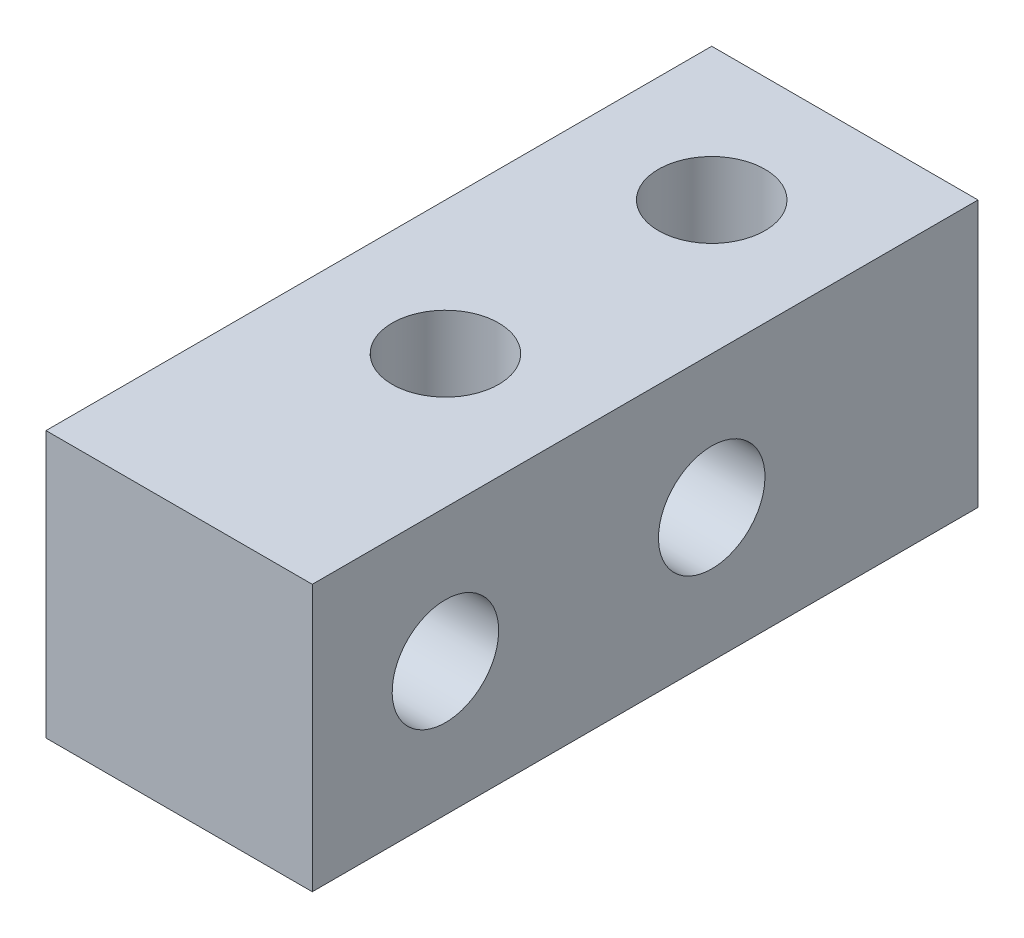
SolidWorks part; units mm, degrees
material "1060 合金"
ref_plane "前视基准面" through (0, 0, 0) normal (0, 0, 1) x (1, 0, 0)
ref_plane "上视基准面" through (0, 0, 0) normal (0, 1, 0) x (1, 0, 0)
ref_plane "右视基准面" through (0, 0, 0) normal (1, 0, 0) x (0, 0, -1)
other "Configuration Table"
sketch "草图1" plane through (0, 0, 0) normal (0, 0, 1) x (1, 0, 0)
  line L1 (-5, 5) -> (5, 5)
  line L2 (-5, 5) -> (-5, -5)
  line L3 (-5, -5) -> (5, -5)
  line L4 (5, 5) -> (5, -5)
  line L5 (-5, 5) -> (5, -5) construction
  line L6 (-5, -5) -> (5, 5) construction
  point P0 (0, 0)
  dimension "D1" = 10
extrude "凸台-拉伸1" add sketch "草图1" along normal mid plane 25
sketch "草图2" plane through (5, 0, 0) normal (1, 0, 0) x (0, 0, -1)
  line L0 (-7.5, 0) -> (2.5, 0) construction
  line L1 (-12.5, -5) -> (-12.5, 5) construction
  line L2 (-7.5, 0) -> (-12.5, 0) construction
  circle A0 centre (-7.5, 0) radius 2
  circle A1 centre (2.5, 0) radius 2
  dimension "D3" = 4
  dimension "D1" = 5
  dimension "D2" = 10
extrude "切除-拉伸1" cut sketch "草图2" against normal blind 25
sketch "草图3" plane through (0, 5, 0) normal (0, 1, 0) x (1, 0, 0)
  line L0 (0, 12.5) -> (0, 7.5) construction
  line L1 (5, 12.5) -> (-5, 12.5) construction
  line L2 (0, 7.5) -> (0, -2.5) construction
  circle A0 centre (0, 7.5) radius 2
  circle A1 centre (0, -2.5) radius 2
  dimension "D3" = 4
  dimension "D1" = 5
  dimension "D2" = 10
extrude "切除-拉伸2" cut sketch "草图3" against normal blind 25
